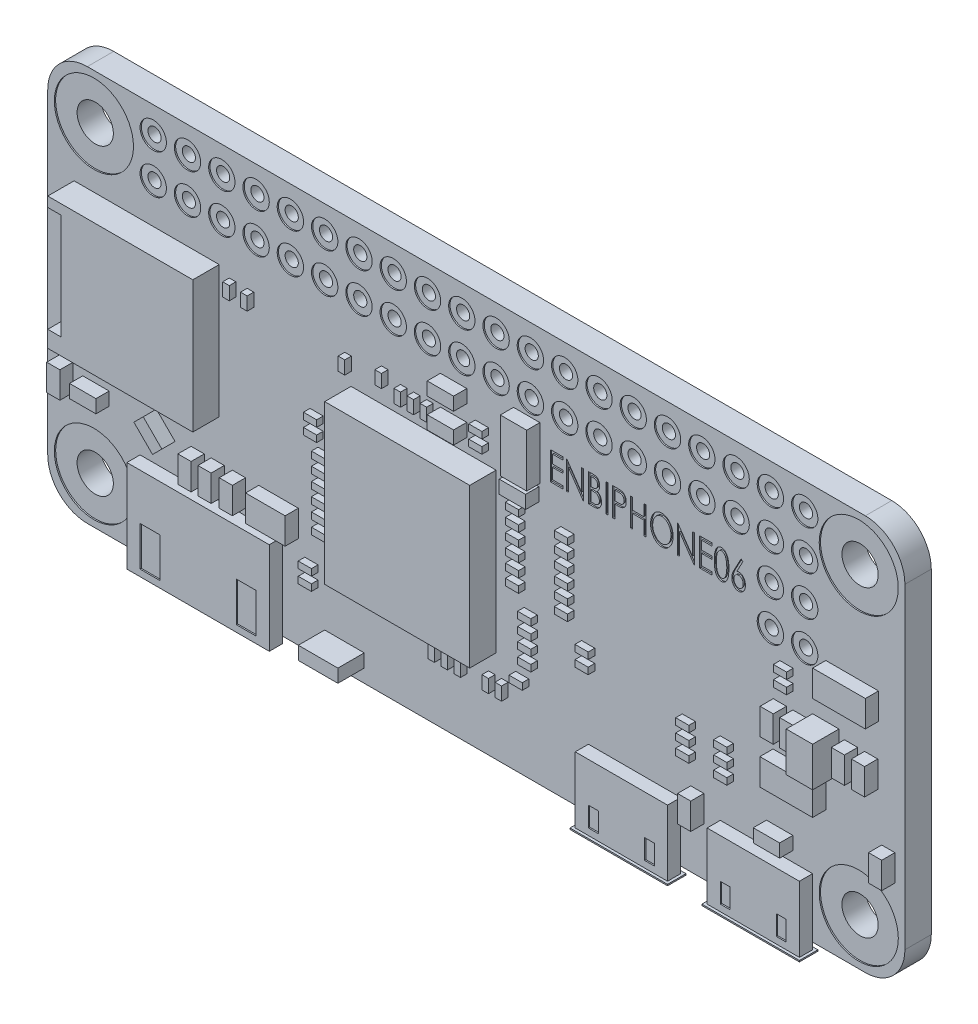
SolidWorks part; units mm, degrees
ref_plane "Front Plane" through (0, 0, 0) normal (0, 0, 1) x (1, 0, 0)
ref_plane "Top Plane" through (0, 0, 0) normal (0, 1, 0) x (1, 0, 0)
ref_plane "Right Plane" through (0, 0, 0) normal (1, 0, 0) x (0, 0, -1)
sketch "Sketch1" plane through (0, 0, 0) normal (0, 0, 1) x (1, 0, 0)
  line L0 (3, 0) -> (62, 0)
  line L1 (65, 3) -> (65, 27)
  line L2 (62, 30) -> (3, 30)
  line L3 (0, 27) -> (0, 3)
  line L4 (32.5, 40.0498) -> (32.5, -5.767) construction
  line L5 (-9.8623, 15) -> (70.5229, 15) construction
  arc A0 (3, 30) -> (0, 27) centre (3, 27) ccw
  arc A1 (65, 27) -> (62, 30) centre (62, 27) ccw
  arc A2 (62, 0) -> (65, 3) centre (62, 3) ccw
  arc A3 (3, 0) -> (0, 3) centre (3, 3) cw
  circle A4 centre (3.5, 26.5) radius 3
  circle A5 centre (61.5, 26.5) radius 3
  circle A6 centre (61.5, 3.5) radius 3
  circle A7 centre (3.5, 3.5) radius 3
  circle A8 centre (3.5, 26.5) radius 1.375
  circle A9 centre (61.5, 26.5) radius 1.375
  circle A10 centre (61.5, 3.5) radius 1.375
  circle A11 centre (3.5, 3.5) radius 1.375
  point P7 (0, 30)
  point P10 (65, 30)
  point P15 (0, 0)
  dimension "D3" = 3
  dimension "D4" = 3
  dimension "D5" = 6
  dimension "D8" = 2.75
  dimension "D1" = 30
  dimension "D2" = 65
  dimension "D6" = 3.5
  dimension "D7" = 3.5
extrude "Boss-Extrude1" add sketch "Sketch1" along normal blind 2 contours A3 L0 A2 L1 A1 L2 A0 L3 A5 A4 A6 A7 | A4 A8 | A7 A11 | A5 A9 | A6 A10
sketch "Sketch2" plane through (0, 0, 2) normal (0, 0, 1) x (1, 0, 0)
  line L0 (32.5, 35.9656) -> (32.5, -1.9312) construction
  line L1 (-5.8713, 15) -> (71.491, 15) construction
  circle A0 centre (3.5, 26.5) radius 3
  circle A1 centre (3.5, 26.5) radius 1.375
  circle A2 centre (61.5, 26.5) radius 1.375
  circle A3 centre (61.5, 26.5) radius 3
  circle A4 centre (61.5, 3.5) radius 1.375
  circle A5 centre (61.5, 3.5) radius 3
  circle A6 centre (3.5, 3.5) radius 1.375
  circle A7 centre (3.5, 3.5) radius 3
  dimension "D1" = 6
extrude "Cut-Extrude1" cut sketch "Sketch2" against normal blind 0.1
sketch "Sketch3" plane through (0, 0, 0) normal (0, 0, -1) x (-1, 0, 0)
  line L0 (-32.5, 35.6796) -> (-32.5, -2.427) construction
  line L1 (-70.0669, 15) -> (3.8712, 15) construction
  circle A0 centre (-61.5, 26.5) radius 3
  circle A1 centre (-61.5, 26.5) radius 1.375
  circle A2 centre (-3.5, 26.5) radius 1.375
  circle A3 centre (-3.5, 26.5) radius 3
  circle A4 centre (-3.5, 3.5) radius 1.375
  circle A5 centre (-3.5, 3.5) radius 3
  circle A6 centre (-61.5, 3.5) radius 1.375
  circle A7 centre (-61.5, 3.5) radius 3
  dimension "D1" = 6
extrude "Cut-Extrude2" cut sketch "Sketch3" against normal blind 0.1
sketch "Sketch4" plane through (0, 0, 2) normal (0, 0, 1) x (1, 0, 0)
  line L0 (51, -0.5) -> (58, -0.5)
  line L1 (58, -0.5) -> (58, 4.5)
  line L2 (58, 4.5) -> (51, 4.5)
  line L3 (51, 4.5) -> (51, -0.5)
  line L4 (65, 3) -> (65, 27) construction
  line L5 (3, 0) -> (62, 0) construction
  line L6 (48, -0.5) -> (48, 4.5)
  line L7 (48, 4.5) -> (41, 4.5)
  line L8 (41, 4.5) -> (41, -0.5)
  line L9 (41, -0.5) -> (48, -0.5)
  dimension "D1" = 7
  dimension "D2" = 7
  dimension "D3" = 0.5
  dimension "D4" = 5
  dimension "D5" = 7
  dimension "D6" = 5
  dimension "D7" = 3
  dimension "D8" = 0.5
extrude "Boss-Extrude2" add sketch "Sketch4" along normal blind 1
sketch "Sketch5" plane through (0, 0, 2) normal (0, 0, 1) x (1, 0, 0)
  line L0 (7, 6.5) -> (7, -0.5)
  line L1 (7, -0.5) -> (17.8, -0.5)
  line L2 (17.8, -0.5) -> (17.8, 6.5)
  line L3 (17.8, 6.5) -> (7, 6.5)
  line L4 (0, 27) -> (0, 3) construction
  line L5 (3, 0) -> (41, 0) construction
  dimension "D1" = 7
  dimension "D2" = 10.8
  dimension "D3" = 0.5
  dimension "D4" = 7
extrude "Boss-Extrude3" add sketch "Sketch5" along normal up to surface (1 mm away) up to face at (44.5, 2, 3)
sketch "Sketch6" plane through (0, -0.5, 0) normal (0, -1, 0) x (1, 0, 0)
  line L0 (40.8, 3.2) -> (48.2, 3.2)
  line L1 (48.2, 3.2) -> (48.2, 1.8)
  line L2 (48.2, 1.8) -> (40.8, 1.8)
  line L3 (40.8, 1.8) -> (40.8, 3.2)
  line L4 (41, 3) -> (48, 3) construction
  line L5 (41, 3) -> (41, 2) construction
  line L6 (41, 2) -> (48, 2) construction
  line L7 (48, 3) -> (48, 2) construction
  line L8 (58.2, 3.2) -> (58.2, 1.8)
  line L9 (50.8, 3.2) -> (58.2, 3.2)
  line L10 (58.2, 1.8) -> (50.8, 1.8)
  line L11 (50.8, 1.8) -> (50.8, 3.2)
  line L12 (58, 3) -> (58, 2) construction
  line L13 (51, 3) -> (51, 2) construction
  dimension "D1" = 0.2
  dimension "D2" = 0.2
  dimension "D3" = 0.2
  dimension "D4" = 0.2
  dimension "D5" = 0.2
  dimension "D6" = 0.2
extrude "Boss-Extrude4" add sketch "Sketch6" along normal blind 0.1
sketch "Sketch7" plane through (0, 0, 2) normal (0, 0, 1) x (1, 0, 0)
  line L0 (62, 30) -> (3, 30) construction
  line L1 (0, 27) -> (0, 3) construction
  line L2 (3.5, 26.5) -> (11.4293, 26.5) construction
  circle A0 centre (8, 28) radius 0.5
  circle A1 centre (8, 25) radius 0.5
  circle A2 centre (10.6, 28) radius 0.5
  circle A3 centre (10.6, 25) radius 0.5
  circle A4 centre (13.2, 28) radius 0.5
  circle A5 centre (13.2, 25) radius 0.5
  circle A6 centre (15.8, 28) radius 0.5
  circle A7 centre (15.8, 25) radius 0.5
  circle A8 centre (18.4, 28) radius 0.5
  circle A9 centre (18.4, 25) radius 0.5
  circle A10 centre (21, 28) radius 0.5
  circle A11 centre (21, 25) radius 0.5
  circle A12 centre (23.6, 28) radius 0.5
  circle A13 centre (23.6, 25) radius 0.5
  circle A14 centre (26.2, 28) radius 0.5
  circle A15 centre (26.2, 25) radius 0.5
  circle A16 centre (28.8, 28) radius 0.5
  circle A17 centre (28.8, 25) radius 0.5
  circle A18 centre (31.4, 28) radius 0.5
  circle A19 centre (31.4, 25) radius 0.5
  circle A20 centre (34, 28) radius 0.5
  circle A21 centre (34, 25) radius 0.5
  circle A22 centre (36.6, 28) radius 0.5
  circle A23 centre (36.6, 25) radius 0.5
  circle A24 centre (39.2, 28) radius 0.5
  circle A25 centre (39.2, 25) radius 0.5
  circle A26 centre (41.8, 28) radius 0.5
  circle A27 centre (41.8, 25) radius 0.5
  circle A28 centre (44.4, 28) radius 0.5
  circle A29 centre (44.4, 25) radius 0.5
  circle A30 centre (47, 28) radius 0.5
  circle A31 centre (47, 25) radius 0.5
  circle A32 centre (49.6, 28) radius 0.5
  circle A33 centre (49.6, 25) radius 0.5
  circle A34 centre (52.2, 28) radius 0.5
  circle A35 centre (52.2, 25) radius 0.5
  circle A36 centre (54.8, 28) radius 0.5
  circle A37 centre (54.8, 25) radius 0.5
  circle A38 centre (57.4, 28) radius 0.5
  circle A39 centre (57.4, 25) radius 0.5
  circle A40 centre (54.8, 22) radius 0.5
  circle A41 centre (57.4, 22) radius 0.5
  circle A42 centre (54.8, 19) radius 0.5
  circle A43 centre (57.4, 19) radius 0.5
  dimension "D1" = 1
  dimension "D2" = 2
  dimension "D3" = 8
  dimension "D4" = 20
extrude "Cut-Extrude3" cut sketch "Sketch7" against normal blind 2
sketch "Sketch8" plane through (0, 0, 2) normal (0, 0, 1) x (1, 0, 0)
  circle A0 centre (8, 28) radius 0.5
  circle A1 centre (8, 28) radius 1
  circle A2 centre (8, 25) radius 0.5
  circle A3 centre (8, 25) radius 1
  circle A4 centre (10.6, 28) radius 1
  circle A5 centre (10.6, 28) radius 0.5
  circle A6 centre (10.6, 25) radius 1
  circle A7 centre (10.6, 25) radius 0.5
  circle A8 centre (13.2, 28) radius 1
  circle A9 centre (13.2, 28) radius 0.5
  circle A10 centre (13.2, 25) radius 1
  circle A11 centre (13.2, 25) radius 0.5
  circle A12 centre (15.8, 28) radius 1
  circle A13 centre (15.8, 28) radius 0.5
  circle A14 centre (15.8, 25) radius 1
  circle A15 centre (15.8, 25) radius 0.5
  circle A16 centre (18.4, 28) radius 1
  circle A17 centre (18.4, 28) radius 0.5
  circle A18 centre (18.4, 25) radius 1
  circle A19 centre (18.4, 25) radius 0.5
  circle A20 centre (21, 28) radius 1
  circle A21 centre (21, 28) radius 0.5
  circle A22 centre (21, 25) radius 1
  circle A23 centre (21, 25) radius 0.5
  circle A24 centre (23.6, 28) radius 1
  circle A25 centre (23.6, 28) radius 0.5
  circle A26 centre (23.6, 25) radius 1
  circle A27 centre (23.6, 25) radius 0.5
  circle A28 centre (26.2, 28) radius 1
  circle A29 centre (26.2, 28) radius 0.5
  circle A30 centre (26.2, 25) radius 1
  circle A31 centre (26.2, 25) radius 0.5
  circle A32 centre (28.8, 28) radius 1
  circle A33 centre (28.8, 28) radius 0.5
  circle A34 centre (28.8, 25) radius 1
  circle A35 centre (28.8, 25) radius 0.5
  circle A36 centre (31.4, 28) radius 1
  circle A37 centre (31.4, 28) radius 0.5
  circle A38 centre (31.4, 25) radius 1
  circle A39 centre (31.4, 25) radius 0.5
  circle A40 centre (34, 28) radius 1
  circle A41 centre (34, 28) radius 0.5
  circle A42 centre (34, 25) radius 1
  circle A43 centre (34, 25) radius 0.5
  circle A44 centre (36.6, 28) radius 1
  circle A45 centre (36.6, 28) radius 0.5
  circle A46 centre (36.6, 25) radius 1
  circle A47 centre (36.6, 25) radius 0.5
  circle A48 centre (39.2, 28) radius 1
  circle A49 centre (39.2, 28) radius 0.5
  circle A50 centre (39.2, 25) radius 1
  circle A51 centre (39.2, 25) radius 0.5
  circle A52 centre (41.8, 28) radius 1
  circle A53 centre (41.8, 28) radius 0.5
  circle A54 centre (41.8, 25) radius 1
  circle A55 centre (41.8, 25) radius 0.5
  circle A56 centre (44.4, 28) radius 1
  circle A57 centre (44.4, 28) radius 0.5
  circle A58 centre (44.4, 25) radius 1
  circle A59 centre (44.4, 25) radius 0.5
  circle A60 centre (47, 28) radius 1
  circle A61 centre (47, 28) radius 0.5
  circle A62 centre (47, 25) radius 1
  circle A63 centre (47, 25) radius 0.5
  circle A64 centre (49.6, 28) radius 1
  circle A65 centre (49.6, 28) radius 0.5
  circle A66 centre (49.6, 25) radius 1
  circle A67 centre (49.6, 25) radius 0.5
  circle A68 centre (52.2, 28) radius 1
  circle A69 centre (52.2, 28) radius 0.5
  circle A70 centre (52.2, 25) radius 1
  circle A71 centre (52.2, 25) radius 0.5
  circle A72 centre (54.8, 28) radius 1
  circle A73 centre (54.8, 28) radius 0.5
  circle A74 centre (54.8, 25) radius 1
  circle A75 centre (54.8, 25) radius 0.5
  circle A76 centre (57.4, 28) radius 1
  circle A77 centre (57.4, 28) radius 0.5
  circle A78 centre (57.4, 25) radius 1
  circle A79 centre (57.4, 25) radius 0.5
  circle A80 centre (57.4, 22) radius 0.5
  circle A81 centre (54.8, 22) radius 1
  circle A82 centre (57.4, 22) radius 1
  circle A83 centre (54.8, 22) radius 0.5
  circle A84 centre (57.4, 19) radius 0.5
  circle A85 centre (54.8, 19) radius 1
  circle A86 centre (57.4, 19) radius 1
  circle A87 centre (54.8, 19) radius 0.5
  dimension "D1" = 2
  dimension "D2" = 2
  dimension "D3" = 20
extrude "Cut-Extrude4" cut sketch "Sketch8" against normal blind 0.1
sketch "Sketch9" plane through (0, 0, 3) normal (0, 0, 1) x (1, 0, 0)
  line L0 (8, 0) -> (8, 3)
  line L1 (8, 3) -> (9.5, 3)
  line L2 (9.5, 3) -> (9.5, 0)
  line L3 (9.5, 0) -> (8, 0)
  line L4 (15.3, 0) -> (15.3, 3)
  line L5 (15.3, 3) -> (16.8, 3)
  line L6 (16.8, 3) -> (16.8, 0)
  line L7 (16.8, 0) -> (15.3, 0)
  line L8 (7, 6.5) -> (7, 0) construction
  line L9 (7, -0.5) -> (17.8, -0.5) construction
  line L10 (17.8, -0.5) -> (17.8, 6.5) construction
  line L11 (42, 0) -> (42.75, 0)
  line L12 (42.75, 0) -> (42.75, 1.5)
  line L13 (42.75, 1.5) -> (42, 1.5)
  line L14 (42, 1.5) -> (42, 0)
  line L15 (46.25, 0) -> (47, 0)
  line L16 (47, 0) -> (47, 1.5)
  line L17 (47, 1.5) -> (46.25, 1.5)
  line L18 (46.25, 1.5) -> (46.25, 0)
  line L19 (57, 0) -> (57, 1.5)
  line L20 (52.75, 1.5) -> (52, 1.5)
  line L21 (57, 1.5) -> (56.25, 1.5)
  line L22 (52, 0) -> (52.75, 0)
  line L23 (52.75, 0) -> (52.75, 1.5)
  line L24 (56.25, 0) -> (57, 0)
  line L25 (56.25, 1.5) -> (56.25, 0)
  line L26 (52, 1.5) -> (52, 0)
  line L27 (41, 4.5) -> (41, -0.5) construction
  line L28 (48, -0.5) -> (48, 4.5) construction
  dimension "D1" = 1.5
  dimension "D2" = 3
  dimension "D3" = 3
  dimension "D4" = 1.5
  dimension "D5" = 1
  dimension "D6" = 0.5
  dimension "D7" = 1
  dimension "D8" = 0.5
  dimension "D9" = 0.75
  dimension "D10" = 1.5
  dimension "D11" = 1
  dimension "D12" = 1
  dimension "D13" = 0.75
  dimension "D14" = 1.5
extrude "Cut-Extrude5" cut sketch "Sketch9" against normal blind 0.1
sketch "Sketch10" plane through (0, 0, 2) normal (0, 0, 1) x (1, 0, 0)
  line L0 (3, 21.25) -> (3, 13.25)
  line L1 (3, 12) -> (13, 12)
  line L2 (13, 12) -> (13, 22)
  line L3 (13, 22) -> (3, 22)
  line L4 (62, 30) -> (3, 30) construction
  line L5 (0, 27) -> (0, 3) construction
  line L6 (23, 19) -> (23, 7)
  line L7 (23, 7) -> (34, 7)
  line L8 (34, 7) -> (34, 19)
  line L9 (34, 19) -> (23, 19)
  line L10 (3, 22) -> (2, 22)
  line L11 (2, 22) -> (2, 21.25)
  line L12 (2, 21.25) -> (3, 21.25)
  line L13 (3, 12) -> (2, 12)
  line L14 (2, 12) -> (2, 13.25)
  line L15 (2, 13.25) -> (3, 13.25)
  line L16 (58, 15) -> (58, 12)
  line L17 (58, 12) -> (60, 12)
  line L18 (60, 12) -> (60, 15)
  line L19 (60, 15) -> (58, 15)
  line L20 (65, 3) -> (65, 27) construction
  line L21 (21, 2) -> (24, 2)
  line L22 (24, 2) -> (24, 1)
  line L23 (24, 1) -> (21, 1)
  line L24 (21, 1) -> (21, 2)
  line L25 (17.8, 0) -> (41, 0) construction
  dimension "D1" = 10
  dimension "D2" = 8
  dimension "D3" = 10
  dimension "D4" = 3
  dimension "D5" = 23
  dimension "D6" = 11
  dimension "D7" = 12
  dimension "D8" = 11
  dimension "D9" = 1
  dimension "D10" = 0.75
  dimension "D11" = 1
  dimension "D12" = 1.25
  dimension "D13" = 2
  dimension "D14" = 5
  dimension "D15" = 3
  dimension "D16" = 15
  dimension "D17" = 3
  dimension "D18" = 1
  dimension "D19" = 1
  dimension "D20" = 21
extrude "Boss-Extrude5" add sketch "Sketch10" along normal blind 2
sketch "Sketch11" plane through (0, 0, 2) normal (0, 0, 1) x (1, 0, 0)
  line L0 (3, 21) -> (2, 21)
  line L1 (3, 21.25) -> (3, 13.25) construction
  line L2 (2, 21) -> (2, 20.5)
  line L3 (2, 20.5) -> (3, 20.5)
  line L4 (3, 20.5) -> (3, 21)
  line L5 (13, 22) -> (2, 22) construction
  line L6 (3, 20) -> (2, 20)
  line L7 (2, 20) -> (2, 19.5)
  line L8 (2, 19.5) -> (3, 19.5)
  line L9 (3, 19.5) -> (3, 20)
  line L10 (3, 19) -> (2, 19)
  line L11 (2, 19) -> (2, 18.5)
  line L12 (2, 18.5) -> (3, 18.5)
  line L13 (3, 18.5) -> (3, 19)
  line L14 (3, 18) -> (2, 18)
  line L15 (2, 18) -> (2, 17.5)
  line L16 (2, 17.5) -> (3, 17.5)
  line L17 (3, 17.5) -> (3, 18)
  line L18 (3, 17) -> (2, 17)
  line L19 (2, 17) -> (2, 16.5)
  line L20 (2, 16.5) -> (3, 16.5)
  line L21 (3, 16.5) -> (3, 17)
  line L22 (3, 16) -> (2, 16)
  line L23 (2, 16) -> (2, 15.5)
  line L24 (2, 15.5) -> (3, 15.5)
  line L25 (3, 15.5) -> (3, 16)
  line L26 (3, 15) -> (2, 15)
  line L27 (2, 15) -> (2, 14.5)
  line L28 (2, 14.5) -> (3, 14.5)
  line L29 (3, 14.5) -> (3, 15)
  line L30 (3, 14) -> (2, 14)
  line L31 (2, 14) -> (2, 13.5)
  line L32 (2, 13.5) -> (3, 13.5)
  line L33 (3, 13.5) -> (3, 14)
  line L34 (19.8884, 16) -> (19.8884, 15.5)
  line L35 (19.8884, 14.5) -> (20.8884, 14.5)
  line L36 (20.8884, 16) -> (19.8884, 16)
  line L37 (20.8884, 14.5) -> (20.8884, 15)
  line L38 (20.8884, 15.5) -> (20.8884, 16)
  line L39 (19.8884, 15.5) -> (20.8884, 15.5)
  line L40 (20.8884, 15) -> (19.8884, 15)
  line L41 (19.8884, 15) -> (19.8884, 14.5)
  line L42 (21.4925, 8.7519) -> (20.4925, 8.7519)
  line L43 (20.4925, 11.7519) -> (20.4925, 11.2519)
  line L44 (20.4925, 12.2519) -> (21.4925, 12.2519)
  line L45 (20.4925, 10.2519) -> (21.4925, 10.2519)
  line L46 (21.4925, 9.2519) -> (21.4925, 9.7519)
  line L47 (21.4925, 12.7519) -> (20.4925, 12.7519)
  line L48 (20.4925, 12.7519) -> (20.4925, 12.2519)
  line L49 (21.4925, 11.7519) -> (20.4925, 11.7519)
  line L50 (21.4925, 10.2519) -> (21.4925, 10.7519)
  line L51 (20.4925, 13.7519) -> (20.4925, 13.2519)
  line L52 (20.4925, 9.7519) -> (20.4925, 9.2519)
  line L53 (21.4925, 11.2519) -> (21.4925, 11.7519)
  line L54 (20.4925, 8.7519) -> (20.4925, 8.2519)
  line L55 (20.4925, 9.2519) -> (21.4925, 9.2519)
  line L56 (21.4925, 13.2519) -> (21.4925, 13.7519)
  line L57 (20.4925, 8.2519) -> (21.4925, 8.2519)
  line L58 (20.4925, 13.2519) -> (21.4925, 13.2519)
  line L59 (21.4925, 12.2519) -> (21.4925, 12.7519)
  line L60 (20.4925, 11.2519) -> (21.4925, 11.2519)
  line L61 (21.4925, 9.7519) -> (20.4925, 9.7519)
  line L62 (21.4925, 13.7519) -> (20.4925, 13.7519)
  line L63 (21.4925, 10.7519) -> (20.4925, 10.7519)
  line L64 (20.4925, 10.7519) -> (20.4925, 10.2519)
  line L65 (21.4925, 8.2519) -> (21.4925, 8.7519)
  line L66 (20.4925, 4.528) -> (20.4925, 5.028)
  line L67 (19.4925, 5.528) -> (20.4925, 5.528)
  line L68 (20.4925, 5.028) -> (19.4925, 5.028)
  line L69 (20.4925, 6.028) -> (19.4925, 6.028)
  line L70 (19.4925, 6.028) -> (19.4925, 5.528)
  line L71 (19.4925, 5.028) -> (19.4925, 4.528)
  line L72 (20.4925, 5.528) -> (20.4925, 6.028)
  line L73 (19.4925, 4.528) -> (20.4925, 4.528)
  line L74 (35.2014, 12.2519) -> (36.2014, 12.2519)
  line L75 (36.2014, 16.2519) -> (36.2014, 16.7519)
  line L76 (35.2014, 16.7519) -> (35.2014, 16.2519)
  line L77 (35.2014, 12.7519) -> (35.2014, 12.2519)
  line L78 (36.2014, 13.7519) -> (35.2014, 13.7519)
  line L79 (36.2014, 13.2519) -> (36.2014, 13.7519)
  line L80 (36.2014, 14.7519) -> (35.2014, 14.7519)
  line L81 (36.2014, 16.7519) -> (35.2014, 16.7519)
  line L82 (36.2014, 12.2519) -> (36.2014, 12.7519)
  line L83 (35.2014, 16.2519) -> (36.2014, 16.2519)
  line L84 (35.2014, 17.7519) -> (35.2014, 17.2519)
  line L85 (36.2014, 17.2519) -> (36.2014, 17.7519)
  line L86 (36.2014, 15.2519) -> (36.2014, 15.7519)
  line L87 (35.2014, 17.2519) -> (36.2014, 17.2519)
  line L88 (35.2014, 14.2519) -> (36.2014, 14.2519)
  line L89 (35.2014, 15.2519) -> (36.2014, 15.2519)
  line L90 (36.2014, 15.7519) -> (35.2014, 15.7519)
  line L91 (36.2014, 17.7519) -> (35.2014, 17.7519)
  line L92 (35.2014, 14.7519) -> (35.2014, 14.2519)
  line L93 (35.2014, 15.7519) -> (35.2014, 15.2519)
  line L94 (36.2014, 14.2519) -> (36.2014, 14.7519)
  line L95 (35.2014, 13.7519) -> (35.2014, 13.2519)
  line L96 (36.2014, 12.7519) -> (35.2014, 12.7519)
  line L97 (35.2014, 13.2519) -> (36.2014, 13.2519)
  line L98 (37.1279, 11.0489) -> (36.1279, 11.0489)
  line L99 (37.1279, 9.5489) -> (37.1279, 10.0489)
  line L100 (37.1279, 10.5489) -> (37.1279, 11.0489)
  line L101 (36.1279, 8.5489) -> (37.1279, 8.5489)
  line L102 (36.1279, 10.5489) -> (37.1279, 10.5489)
  line L103 (37.1279, 7.5489) -> (37.1279, 8.0489)
  line L104 (37.1279, 10.0489) -> (36.1279, 10.0489)
  line L105 (36.1279, 11.0489) -> (36.1279, 10.5489)
  line L106 (37.1279, 8.5489) -> (37.1279, 9.0489)
  line L107 (36.1279, 9.0489) -> (36.1279, 8.5489)
  line L108 (36.1279, 8.0489) -> (36.1279, 7.5489)
  line L109 (36.1279, 10.0489) -> (36.1279, 9.5489)
  line L110 (36.1279, 7.5489) -> (37.1279, 7.5489)
  line L111 (37.1279, 9.0489) -> (36.1279, 9.0489)
  line L112 (37.1279, 8.0489) -> (36.1279, 8.0489)
  line L113 (36.1279, 9.5489) -> (37.1279, 9.5489)
  line L114 (36.4834, 6.028) -> (36.4834, 6.528)
  line L115 (36.4834, 6.528) -> (35.4834, 6.528)
  line L116 (35.4834, 6.528) -> (35.4834, 6.028)
  line L117 (35.4834, 6.028) -> (36.4834, 6.028)
  line L118 (55.5241, 15.7519) -> (56.5241, 15.7519)
  line L119 (56.5241, 16.7519) -> (56.5241, 17.2519)
  line L120 (55.5241, 16.2519) -> (55.5241, 15.7519)
  line L121 (56.5241, 17.2519) -> (55.5241, 17.2519)
  line L122 (56.5241, 16.2519) -> (55.5241, 16.2519)
  line L123 (55.5241, 17.2519) -> (55.5241, 16.7519)
  line L124 (55.5241, 16.7519) -> (56.5241, 16.7519)
  line L125 (56.5241, 15.7519) -> (56.5241, 16.2519)
  line L126 (48.1158, 9.0489) -> (48.1158, 8.5489)
  line L127 (48.1158, 10.0489) -> (48.1158, 9.5489)
  line L128 (49.1158, 9.5489) -> (49.1158, 10.0489)
  line L129 (49.1158, 9.0489) -> (48.1158, 9.0489)
  line L130 (48.1158, 9.5489) -> (49.1158, 9.5489)
  line L131 (49.1158, 7.5489) -> (49.1158, 8.0489)
  line L132 (49.1158, 8.0489) -> (48.1158, 8.0489)
  line L133 (48.1158, 8.0489) -> (48.1158, 7.5489)
  line L134 (48.1158, 7.5489) -> (49.1158, 7.5489)
  line L135 (49.1158, 10.0489) -> (48.1158, 10.0489)
  line L136 (48.1158, 8.5489) -> (49.1158, 8.5489)
  line L137 (49.1158, 8.5489) -> (49.1158, 9.0489)
  line L138 (50.9942, 9.0489) -> (50.9942, 8.5489)
  line L139 (50.9942, 10.0489) -> (50.9942, 9.5489)
  line L140 (51.9942, 9.5489) -> (51.9942, 10.0489)
  line L141 (51.9942, 9.0489) -> (50.9942, 9.0489)
  line L142 (50.9942, 9.5489) -> (51.9942, 9.5489)
  line L143 (51.9942, 7.5489) -> (51.9942, 8.0489)
  line L144 (51.9942, 8.0489) -> (50.9942, 8.0489)
  line L145 (50.9942, 8.0489) -> (50.9942, 7.5489)
  line L146 (50.9942, 7.5489) -> (51.9942, 7.5489)
  line L147 (51.9942, 10.0489) -> (50.9942, 10.0489)
  line L148 (50.9942, 8.5489) -> (51.9942, 8.5489)
  line L149 (51.9942, 8.5489) -> (51.9942, 9.0489)
  line L150 (34.4127, 5.528) -> (34.4127, 4.528)
  line L151 (34.4127, 4.528) -> (34.9127, 4.528)
  line L152 (34.9127, 4.528) -> (34.9127, 5.528)
  line L153 (34.9127, 5.528) -> (34.4127, 5.528)
  line L154 (33.4217, 4.528) -> (33.9217, 4.528)
  line L155 (33.9217, 5.528) -> (33.4217, 5.528)
  line L156 (33.4217, 5.528) -> (33.4217, 4.528)
  line L157 (33.9217, 4.528) -> (33.9217, 5.528)
  line L162 (31.2983, 5.528) -> (31.2983, 4.528)
  line L163 (31.7983, 5.528) -> (31.2983, 5.528)
  line L164 (31.2983, 4.528) -> (31.7983, 4.528)
  line L165 (31.7983, 4.528) -> (31.7983, 5.528)
  line L166 (29.8165, 4.528) -> (29.8165, 5.528)
  line L167 (29.8165, 5.528) -> (29.3165, 5.528)
  line L168 (29.3165, 5.528) -> (29.3165, 4.528)
  line L169 (29.3165, 4.528) -> (29.8165, 4.528)
  line L170 (30.3074, 5.528) -> (30.3074, 4.528)
  line L171 (30.8074, 5.528) -> (30.3074, 5.528)
  line L172 (30.3074, 4.528) -> (30.8074, 4.528)
  line L173 (30.8074, 4.528) -> (30.8074, 5.528)
  line L174 (29.2312, 20) -> (29.2312, 21)
  line L175 (29.2312, 21) -> (28.7312, 21)
  line L176 (28.7312, 20) -> (29.2312, 20)
  line L177 (27.2494, 20) -> (27.2494, 21)
  line L178 (28.7312, 21) -> (28.7312, 20)
  line L179 (26.7494, 21) -> (26.7494, 20)
  line L183 (27.7403, 20) -> (28.2403, 20)
  line L184 (27.2494, 21) -> (26.7494, 21)
  line L185 (26.7494, 20) -> (27.2494, 20)
  line L187 (28.2403, 20) -> (28.2403, 21)
  line L188 (28.2403, 21) -> (27.7403, 21)
  line L189 (27.7403, 21) -> (27.7403, 20)
  line L190 (25.8056, 20.5) -> (25.8056, 21.5)
  line L191 (25.3056, 20.5) -> (25.8056, 20.5)
  line L192 (25.3056, 21.5) -> (25.3056, 20.5)
  line L193 (25.8056, 21.5) -> (25.3056, 21.5)
  line L194 (23.0216, 20) -> (23.0216, 21)
  line L195 (22.5216, 20) -> (23.0216, 20)
  line L196 (22.5216, 21) -> (22.5216, 20)
  line L197 (23.0216, 21) -> (22.5216, 21)
  line L198 (38.9144, 15.7519) -> (38.9144, 15.2519)
  line L199 (39.9144, 17.2519) -> (39.9144, 17.7519)
  line L200 (38.9144, 13.7519) -> (38.9144, 13.2519)
  line L201 (38.9144, 16.7519) -> (38.9144, 16.2519)
  line L202 (38.9144, 13.2519) -> (39.9144, 13.2519)
  line L203 (39.9144, 16.2519) -> (39.9144, 16.7519)
  line L204 (38.9144, 12.7519) -> (38.9144, 12.2519)
  line L205 (39.9144, 13.2519) -> (39.9144, 13.7519)
  line L206 (38.9144, 14.2519) -> (39.9144, 14.2519)
  line L207 (39.9144, 16.7519) -> (38.9144, 16.7519)
  line L208 (39.9144, 15.7519) -> (38.9144, 15.7519)
  line L209 (38.9144, 17.7519) -> (38.9144, 17.2519)
  line L210 (38.9144, 14.7519) -> (38.9144, 14.2519)
  line L211 (39.9144, 14.2519) -> (39.9144, 14.7519)
  line L212 (39.9144, 12.7519) -> (38.9144, 12.7519)
  line L213 (38.9144, 12.2519) -> (39.9144, 12.2519)
  line L214 (39.9144, 15.2519) -> (39.9144, 15.7519)
  line L215 (39.9144, 13.7519) -> (38.9144, 13.7519)
  line L216 (39.9144, 14.7519) -> (38.9144, 14.7519)
  line L217 (38.9144, 17.2519) -> (39.9144, 17.2519)
  line L218 (39.9144, 12.2519) -> (39.9144, 12.7519)
  line L219 (38.9144, 15.2519) -> (39.9144, 15.2519)
  line L220 (38.9144, 16.2519) -> (39.9144, 16.2519)
  line L221 (39.9144, 17.7519) -> (38.9144, 17.7519)
  line L222 (41.4807, 10.0489) -> (40.4807, 10.0489)
  line L223 (40.4807, 10.0489) -> (40.4807, 9.5489)
  line L224 (41.4807, 11.0489) -> (40.4807, 11.0489)
  line L225 (40.4807, 11.0489) -> (40.4807, 10.5489)
  line L226 (41.4807, 10.5489) -> (41.4807, 11.0489)
  line L227 (40.4807, 9.5489) -> (41.4807, 9.5489)
  line L228 (40.4807, 10.5489) -> (41.4807, 10.5489)
  line L229 (41.4807, 9.5489) -> (41.4807, 10.0489)
  line L230 (32.4217, 21.5) -> (32.4217, 21)
  line L231 (33.4217, 20.5) -> (32.4217, 20.5)
  line L232 (32.4217, 21) -> (33.4217, 21)
  line L233 (32.4217, 20.5) -> (32.4217, 20)
  line L234 (32.4217, 20) -> (33.4217, 20)
  line L235 (33.4217, 21) -> (33.4217, 21.5)
  line L236 (33.4217, 20) -> (33.4217, 20.5)
  line L237 (33.4217, 21.5) -> (32.4217, 21.5)
  line L238 (14.2649, 21.5) -> (13.7649, 21.5)
  line L239 (13.7649, 21.5) -> (13.7649, 20.5)
  line L240 (13.7649, 20.5) -> (14.2649, 20.5)
  line L241 (14.2649, 20.5) -> (14.2649, 21.5)
  line L242 (15.6224, 21.5) -> (15.1224, 21.5)
  line L243 (15.1224, 21.5) -> (15.1224, 20.5)
  line L244 (15.1224, 20.5) -> (15.6224, 20.5)
  line L245 (15.6224, 20.5) -> (15.6224, 21.5)
  dimension "D1" = 0.5
  dimension "D2" = 1
  dimension "D3" = 1
  dimension "D4" = 8
extrude "Boss-Extrude6" add sketch "Sketch11" along normal blind 0.5
sketch "Sketch12" plane through (0, 0, 2) normal (0, 0, 1) x (1, 0, 0)
  line L0 (57.5, 14.5) -> (57.5, 12.5)
  line L1 (57.5, 12.5) -> (56.5, 12.5)
  line L2 (56.5, 12.5) -> (56.5, 14.5)
  line L3 (56.5, 14.5) -> (57.5, 14.5)
  line L4 (58, 12) -> (60, 12) construction
  line L5 (58, 15) -> (58, 12) construction
  line L6 (56.016, 12.5) -> (55.016, 12.5)
  line L7 (56.016, 14.5) -> (56.016, 12.5)
  line L8 (55.016, 12.5) -> (55.016, 14.5)
  line L9 (55.016, 14.5) -> (56.016, 14.5)
  line L10 (61.4156, 12.5) -> (60.4156, 12.5)
  line L11 (61.4156, 14.5) -> (61.4156, 12.5)
  line L12 (60.4156, 12.5) -> (60.4156, 14.5)
  line L13 (60.4156, 14.5) -> (61.4156, 14.5)
  line L14 (62.941, 12.5) -> (61.941, 12.5)
  line L15 (62.941, 14.5) -> (62.941, 12.5)
  line L16 (61.941, 12.5) -> (61.941, 14.5)
  line L17 (61.941, 14.5) -> (62.941, 14.5)
  line L18 (49.7581, 5.6446) -> (49.7581, 3.6446)
  line L19 (49.7581, 3.6446) -> (48.7581, 3.6446)
  line L20 (48.7581, 5.6446) -> (49.7581, 5.6446)
  line L21 (48.7581, 3.6446) -> (48.7581, 5.6446)
  line L22 (54.5, 6.2648) -> (56.5, 6.2648)
  line L23 (56.5, 6.2648) -> (56.5, 5.2648)
  line L24 (54.5, 5.2648) -> (54.5, 6.2648)
  line L25 (56.5, 5.2648) -> (54.5, 5.2648)
  line L26 (29.7754, 20.0272) -> (29.7754, 21.0272)
  line L27 (29.7754, 21.0272) -> (31.7754, 21.0272)
  line L28 (31.7754, 21.0272) -> (31.7754, 20.0272)
  line L29 (31.7754, 20.0272) -> (29.7754, 20.0272)
  line L30 (29.7754, 22.2475) -> (29.7754, 23.2475)
  line L31 (29.7754, 23.2475) -> (31.7754, 23.2475)
  line L32 (31.7754, 23.2475) -> (31.7754, 22.2475)
  line L33 (31.7754, 22.2475) -> (29.7754, 22.2475)
  line L34 (35.2363, 18.527) -> (35.2363, 19.527)
  line L35 (35.2363, 19.527) -> (37.2363, 19.527)
  line L36 (37.2363, 19.527) -> (37.2363, 18.527)
  line L37 (37.2363, 18.527) -> (35.2363, 18.527)
  line L38 (63.2406, 7) -> (63.2406, 9)
  line L39 (64.2406, 7) -> (63.2406, 7)
  line L40 (64.2406, 9) -> (64.2406, 7)
  line L41 (63.2406, 9) -> (64.2406, 9)
  line L42 (0.922, 8.0488) -> (0.922, 10.0488)
  line L43 (1.922, 8.0488) -> (0.922, 8.0488)
  line L44 (1.922, 10.0488) -> (1.922, 8.0488)
  line L45 (0.922, 10.0488) -> (1.922, 10.0488)
  line L46 (16, 7) -> (19, 7)
  line L47 (19, 7) -> (19, 9)
  line L48 (19, 9) -> (16, 9)
  line L49 (16, 9) -> (16, 7)
  line L50 (17.8, 0) -> (41, 0) construction
  line L51 (0, 27) -> (0, 3) construction
  dimension "D1" = 1
  dimension "D2" = 2
  dimension "D3" = 0.5
  dimension "D4" = 0.5
  dimension "D5" = 2
  dimension "D6" = 3
  dimension "D7" = 7
  dimension "D8" = 16
extrude "Boss-Extrude7" add sketch "Sketch12" along normal blind 1
sketch "Sketch13" plane through (0, 0, 2) normal (0, 0, 1) x (1, 0, 0)
  line L0 (59, 19) -> (59, 17)
  line L1 (59, 17) -> (63, 17)
  line L2 (63, 17) -> (63, 19)
  line L3 (63, 19) -> (59, 19)
  line L4 (65, 3) -> (65, 27) construction
  line L5 (62, 30) -> (3, 30) construction
  line L6 (59, 11.1863) -> (55, 11.1863)
  line L7 (59, 9.1863) -> (59, 11.1863)
  line L8 (55, 11.1863) -> (55, 9.1863)
  line L9 (55, 9.1863) -> (59, 9.1863)
  line L10 (35.3188, 23.7821) -> (35.3188, 19.7821)
  line L11 (37.3188, 23.7821) -> (35.3188, 23.7821)
  line L12 (35.3188, 19.7821) -> (37.3188, 19.7821)
  line L13 (37.3188, 19.7821) -> (37.3188, 23.7821)
  dimension "D1" = 2
  dimension "D2" = 4
  dimension "D3" = 2
  dimension "D4" = 11
extrude "Boss-Extrude8" add sketch "Sketch13" along normal blind 1
sketch "Sketch14" plane through (0, 0, 2) normal (0, 0, 1) x (1, 0, 0)
  line L0 (15, 7) -> (15, 9)
  line L1 (15, 9) -> (14, 9)
  line L2 (14, 9) -> (14, 7)
  line L3 (14, 7) -> (15, 7)
  line L4 (16, 9) -> (16, 7) construction
  line L5 (17.8, 0) -> (41, 0) construction
  line L6 (13.388, 7) -> (13.388, 9)
  line L7 (12.388, 7) -> (13.388, 7)
  line L8 (13.388, 9) -> (12.388, 9)
  line L9 (12.388, 9) -> (12.388, 7)
  line L10 (11.8682, 7) -> (11.8682, 9)
  line L11 (10.8682, 7) -> (11.8682, 7)
  line L12 (11.8682, 9) -> (10.8682, 9)
  line L13 (10.8682, 9) -> (10.8682, 7)
  line L14 (9.6533, 8.7071) -> (8.239, 10.1213)
  line L15 (8.9461, 8) -> (9.6533, 8.7071)
  line L16 (8.239, 10.1213) -> (7.5319, 9.4142)
  line L17 (7.5319, 9.4142) -> (8.9461, 8)
  line L18 (4.655, 8.5211) -> (4.655, 9.5211)
  line L19 (2.655, 8.5211) -> (4.655, 8.5211)
  line L20 (4.655, 9.5211) -> (2.655, 9.5211)
  line L21 (2.655, 9.5211) -> (2.655, 8.5211)
  dimension "D1" = 1
  dimension "D2" = 1
  dimension "D3" = 2
  dimension "D4" = 7
extrude "Boss-Extrude9" add sketch "Sketch14" along normal blind 1
sketch "Sketch15" plane through (0, 0, 2) normal (0, 0, 1) x (1, 0, 0)
  text T0 "ENBIPHONE06" font "Century Gothic" height in points 8
extrude "Cut-Extrude6" cut sketch "Sketch15" against normal blind 0.1
